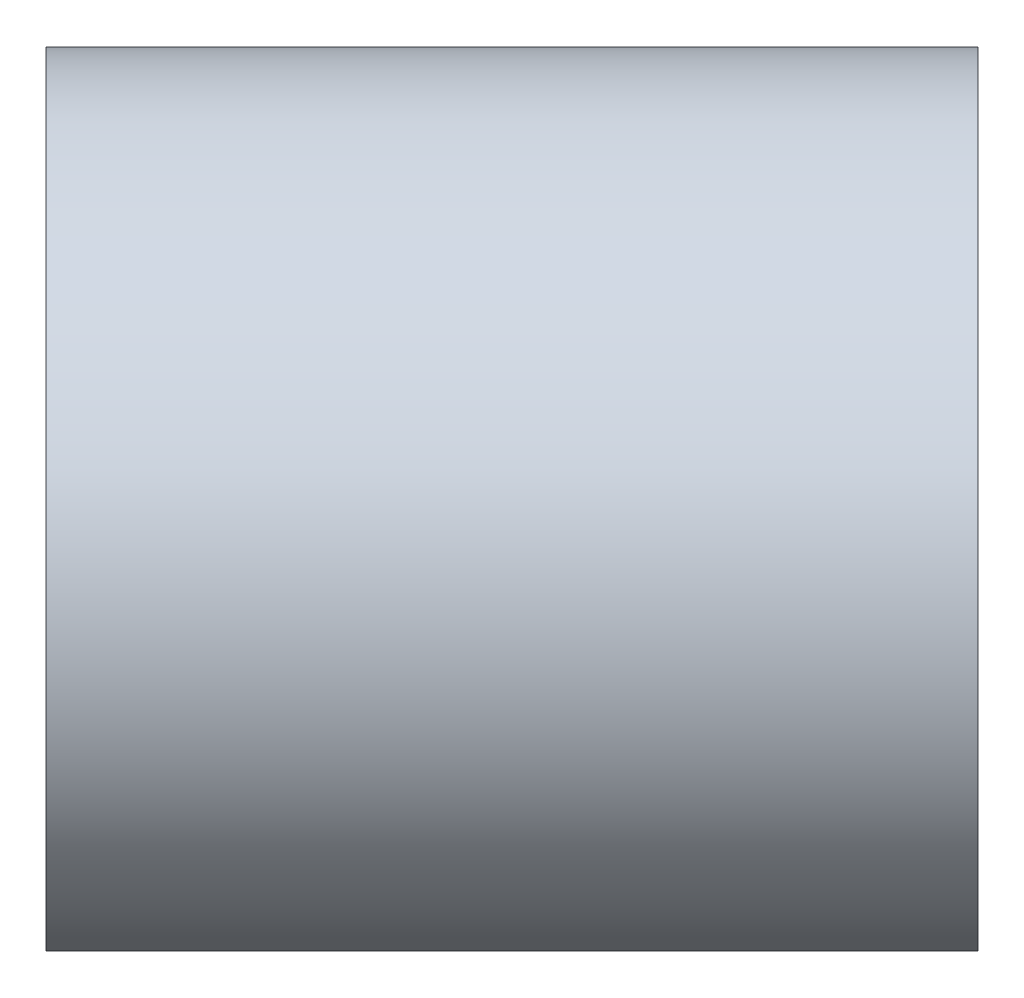
SolidWorks part; units mm, degrees
ref_plane "Front Plane" through (0, 0, 0) normal (0, 0, 1) x (1, 0, 0)
ref_plane "Top Plane" through (0, 0, 0) normal (0, 1, 0) x (1, 0, 0)
ref_plane "Right Plane" through (0, 0, 0) normal (1, 0, 0) x (0, 0, -1)
ref_plane "Plane1" through (155.8554, 0, -155.8554) normal (0.7071, 0, -0.7071) x (-0.7071, 0, -0.7071)
sketch "Sketch1" plane through (155.8554, 0, -155.8554) normal (0.7071, 0, -0.7071) x (-0.7071, 0, -0.7071)
  circle B0 centre (558.5079, -7.5) radius 49
sketch_block_instance "Block1-1"
sketch_block "Block1"
extrude "Boss-Extrude1" add sketch "Sketch1" against normal blind 101
